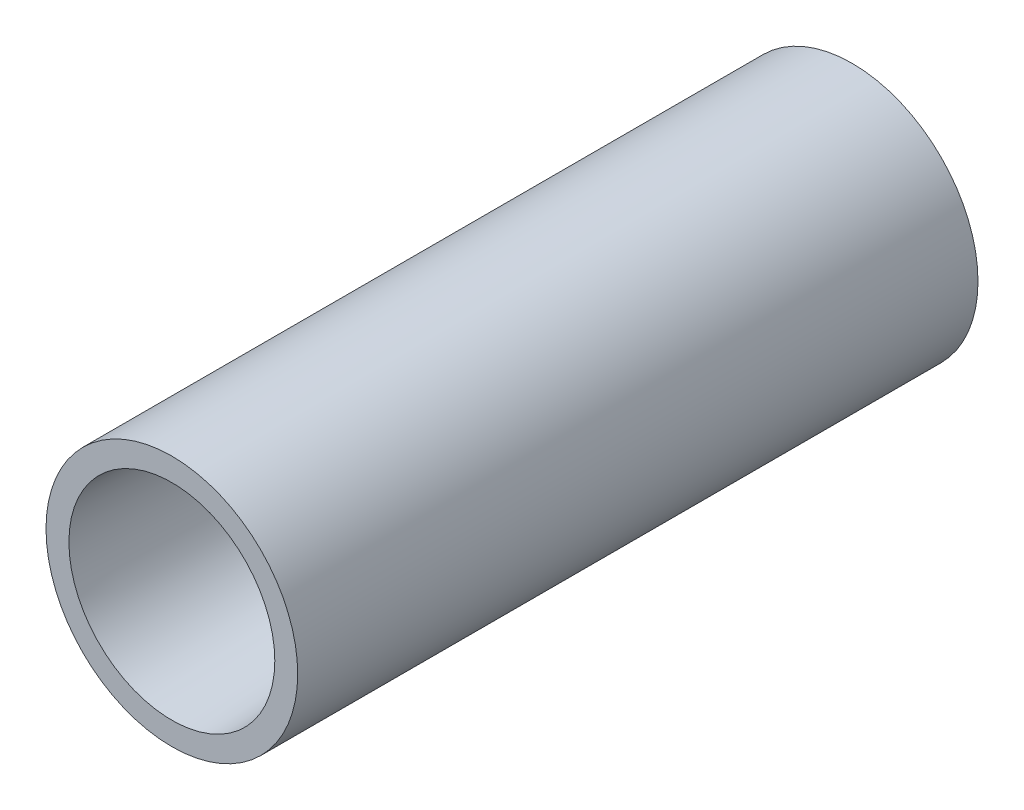
SolidWorks part; units mm, degrees
ref_plane "Front Plane" through (0, 0, 0) normal (0, 0, 1) x (1, 0, 0)
ref_plane "Top Plane" through (0, 0, 0) normal (0, 1, 0) x (1, 0, 0)
ref_plane "Right Plane" through (0, 0, 0) normal (1, 0, 0) x (0, 0, -1)
sketch "Sketch1" plane through (0, 0, 0) normal (0, 0, 1) x (1, 0, 0)
  circle A0 centre (0, 0) radius 2.775
  dimension "D1" = 5.55
extrude "Boss-Extrude1" add sketch "Sketch1" along normal blind 15
sketch "Sketch2" plane through (0, 0, 0) normal (0, 0, 1) x (1, 0, 0)
  circle A0 centre (0, 0) radius 2.27
  dimension "D1" = 4.54
extrude "Cut-Extrude1" cut sketch "Sketch2" along a picked direction on the side of the normal blind 5.68 draft 3.074
sketch "Sketch7" plane through (0, 0, 0) normal (0, 0, 1) x (1, 0, 0)
  circle A0 centre (0, 0) radius 1
extrude "Cut-Extrude2" cut sketch "Sketch7" along normal through all
sketch "Sketch9" plane through (0, 0, 15) normal (0, 0, 1) x (1, 0, 0)
  circle A0 centre (0, 0) radius 2.27
  circle A1 centre (0, 0) radius 2.27 construction
extrude "Cut-Extrude3" cut sketch "Sketch9" against normal blind 5.68 draft 3.074
